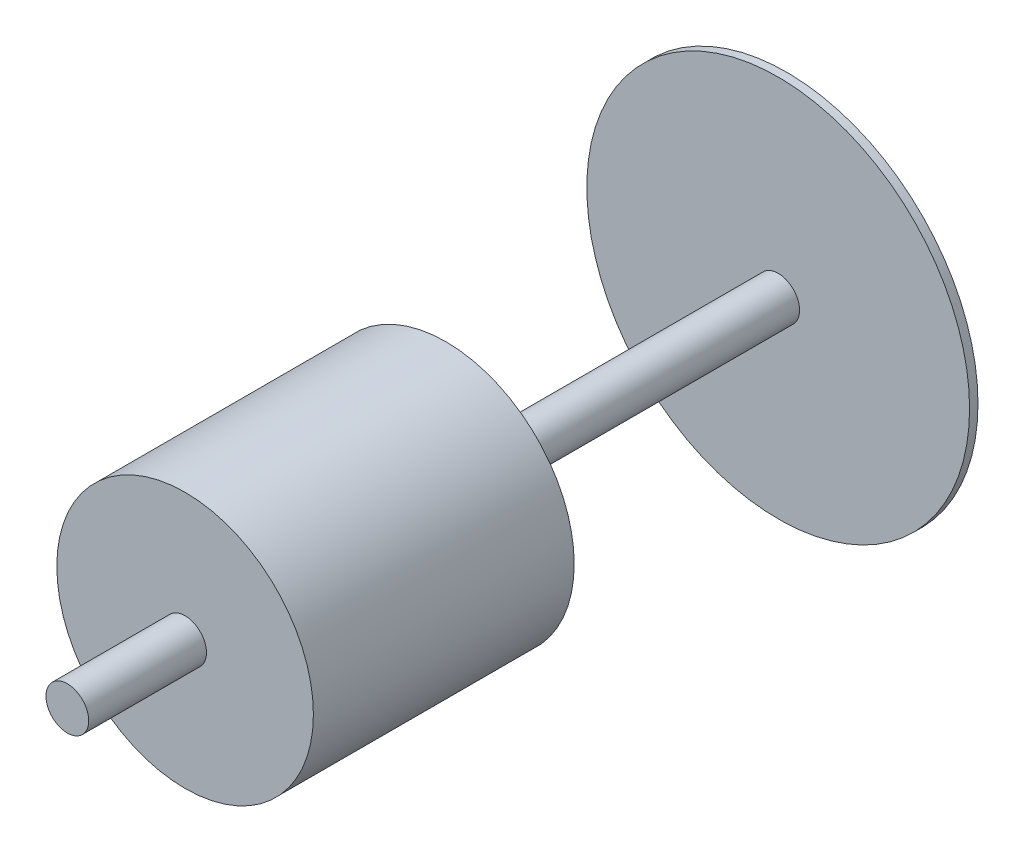
SolidWorks part; units mm, degrees
other "Markup1"
sketch "Sketch6" plane through (500, -500, -1363.6) normal (1, 0, 0) x (0, 0, -1)
ref_plane "Top Plane" through (0, 0, 0) normal (0, 0, 1) x (1, 0, 0)
ref_plane "Right Plane" through (0, 0, 0) normal (0, 1, 0) x (1, 0, 0)
ref_plane "Front Plane" through (0, 0, 0) normal (1, 0, 0) x (0, 0, -1)
sketch "Sketch1" plane through (0, 0, 0) normal (0, 0, 1) x (1, 0, 0)
  circle A0 centre (0, 0) radius 50.8
  dimension "D1" = 101.6
extrude "Boss-Extrude1" add sketch "Sketch1" against normal blind 680 and the other way blind 1030
sketch "Sketch2" plane through (0, 0, -680) normal (0, 0, 1) x (1, 0, 0)
  circle A0 centre (0, 0) radius 455
  dimension "D1" = 910
extrude "Boss-Extrude2" add sketch "Sketch2" along normal blind 20
sketch "Sketch3" plane through (0, 0, -660) normal (0, 0, 1) x (1, 0, 0)
  circle A0 centre (0, 0) radius 222.25
  dimension "D1" = 444.5
sketch "Sketch7" plane through (0, 0, 1030) normal (0, 0, 1) x (1, 0, 0)
  circle A0 centre (0, 0) radius 305
extrude "Boss-Extrude3" add sketch "Sketch7" along a picked direction on the side against the normal blind 620 from offset 280 offset against normal yes
sketch "Sketch8" plane through (0, 0, 130) normal (0, 0, -1) x (-1, 0, 0)
  circle A0 centre (0, 0) radius 225
extrude "Boss-Extrude4" add sketch "Sketch8" along normal blind 50
